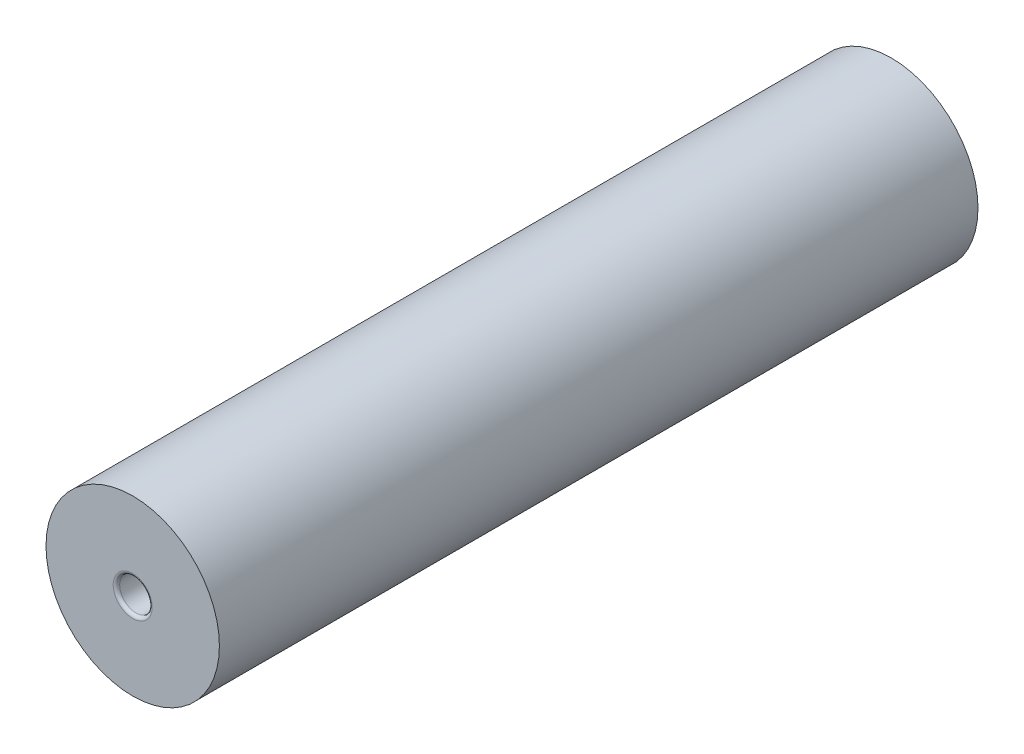
SolidWorks part; units mm, degrees
ref_plane "前视基准面" through (0, 0, 0) normal (0, 0, 1) x (1, 0, 0)
ref_plane "上视基准面" through (0, 0, 0) normal (0, 1, 0) x (1, 0, 0)
ref_plane "右视基准面" through (0, 0, 0) normal (1, 0, 0) x (0, 0, -1)
other "Configuration Table"
sketch "草图1" plane through (0, 0, 0) normal (0, 0, 1) x (1, 0, 0)
  circle A0 centre (0, 0) radius 8
  dimension "D1" = 16
extrude "凸台-拉伸1" add sketch "草图1" against normal blind 70
sketch "草图6" plane through (0, 0, 0) normal (0, 0, 1) x (1, 0, 0)
  circle A0 centre (0, 0) radius 1.5
  dimension "D1" = 3
extrude "切除-拉伸1" cut sketch "草图6" against normal through all
fillet "圆角1" radius 0.3 2 edges at (1.5, 0, -70) (1.5, 0, 0)
